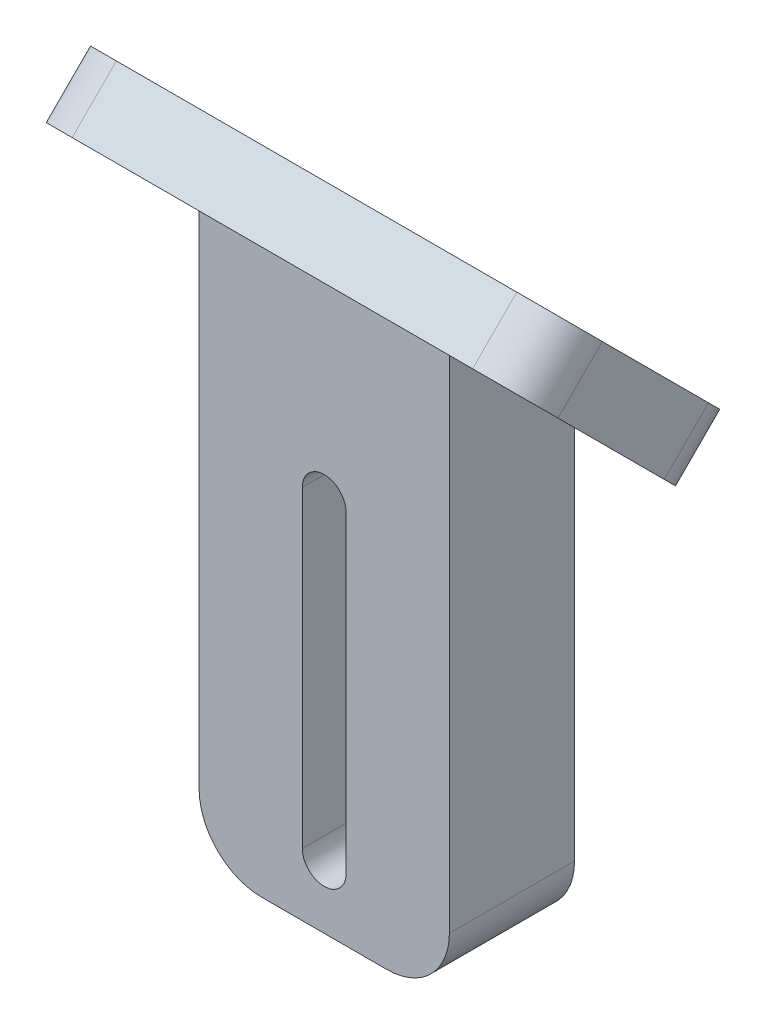
SolidWorks part; units mm, degrees
ref_plane "Front Plane" through (0, 0, 0) normal (0, 0, 1) x (1, 0, 0)
ref_plane "Top Plane" through (0, 0, 0) normal (0, 1, 0) x (1, 0, 0)
ref_plane "Right Plane" through (0, 0, 0) normal (1, 0, 0) x (0, 0, -1)
sketch "Sketch1" plane through (0, 0, 0) normal (1, 0, 0) x (0, 0, -1)
  line L4 (0, 0) -> (0, -35)
  line L5 (0, -35) -> (-10, -35)
  line L6 (-10, -35) -> (-10, 10)
  line L9 (-10, 10) -> (0, 0)
  dimension "D1" = 45
  dimension "D2" = 45
  dimension "D3" = 10
extrude "Boss-Extrude1" add sketch "Sketch1" along normal mid plane 20
sketch "Sketch2" plane through (0, 0, 10) normal (0, 0, 1) x (1, 0, 0)
  line L0 (0, -5) -> (0, -30) construction
  line L1 (1.75, -5) -> (1.75, -30)
  line L2 (-1.75, -5) -> (-1.75, -30)
  line L3 (10, -35) -> (-10, -35) construction
  arc A0 (1.75, -5) -> (-1.75, -5) centre (0, -5) ccw
  arc A1 (-1.75, -30) -> (1.75, -30) centre (0, -30) ccw
  point P3 (0, -17.5)
  point P8 (0, -26.9783)
  point P11 (0, 0)
  point P12 (0, 0)
  point P13 (0, -4.48)
  dimension "D1" = 3.5
  dimension "D2" = 5
  dimension "D3" = 5
extrude "Cut-Extrude1" cut sketch "Sketch2" against normal through all
fillet "Fillet1" radius 5 2 edges at (10, -35, 5) (-10, -35, 5)
sketch "Sketch3" plane through (0, 0, 0) normal (0, 0.7071, -0.7071) x (1, 0, 0)
  line L13 (-20, 0) -> (20, 0)
  line L14 (-20, 0) -> (-20, -20)
  line L15 (-20, -20) -> (20, -20)
  line L16 (20, 0) -> (20, -20)
  line L18 (-10, 0) -> (-10, -14.1421) construction
  line L19 (10, 0) -> (10, -14.1421) construction
  line L21 (10, 0) -> (-10, 0) construction
  dimension "D1" = 10
  dimension "D2" = 10
  dimension "D3" = 20
extrude "Boss-Extrude2" add sketch "Sketch3" along normal blind 5
sketch "Sketch4" plane through (0, 0, 0) normal (0, -0.7071, 0.7071) x (1, 0, 0)
  line L0 (-15, 20) -> (-15, 0) construction
  line L2 (-10, 0) -> (-20, 0) construction
  line L3 (15, 20) -> (15, 0) construction
  line L5 (20, 0) -> (10, 0) construction
  line L6 (-20, 20) -> (20, 20) construction
  circle A0 centre (-15, 10) radius 1.75
  circle A1 centre (15, 10) radius 1.75
  point P4 (-20, 20)
  point P11 (20, 20)
  point P16 (20, 7.0711)
  dimension "D1" = 3.5
  dimension "D2" = 3.5
extrude "Cut-Extrude2" cut sketch "Sketch4" against normal through all
fillet "Fillet2" radius 4 4 edges at (20, 1.7678, -1.7678) (-20, 1.7678, -1.7678) (20, 15.9099, 12.3744) (-20, 15.9099, 12.3744)
